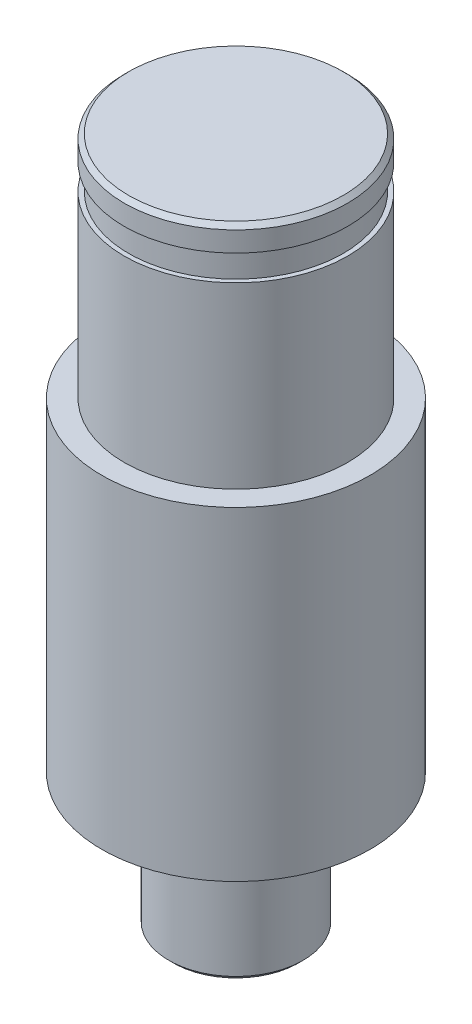
SolidWorks part; units mm, degrees
material "AISI 304"
ref_plane "前基準面" through (0, 0, 0) normal (0, 0, 1) x (1, 0, 0)
ref_plane "上基準面" through (0, 0, 0) normal (0, 1, 0) x (1, 0, 0)
ref_plane "右基準面" through (0, 0, 0) normal (1, 0, 0) x (0, 0, -1)
sketch "草圖1" plane through (0, 0, 0) normal (0, 0, 1) x (1, 0, 0)
  line L0 (0, 0) -> (0, 73.9438) construction
  line L1 (3, 0) -> (3, -6)
  line L2 (3, 0) -> (6, 0)
  line L3 (0, 24.75) -> (5, 24.75)
  line L4 (5, 14.5) -> (6, 14.5)
  line L5 (6, 0) -> (6, 14.5)
  line L6 (0, 24.75) -> (0, -6)
  line L7 (0, -6) -> (3, -6)
  line L8 (5, 24.75) -> (5, 23.65)
  line L9 (5, 22.5) -> (5, 14.5)
  line L10 (5, 23.65) -> (4.8, 23.65)
  line L12 (5, 22.5) -> (4.8, 22.5)
  line L13 (4.8, 23.65) -> (4.8, 22.5)
  dimension "D1" = 6
  dimension "D2" = 12
  dimension "D3" = 14.5
  dimension "D4" = 10
  dimension "D5" = 1.1
  dimension "D6" = 8
  dimension "D7" = 1.15
  dimension "D8" = 9.6
  dimension "D9" = 6
revolve "旋轉1" add sketch "草圖1" angle 360 about L0
chamfer "導角1" distance 0.2 angle 45 2 edges at (0, 24.75, -5) (0, -6, -3)
